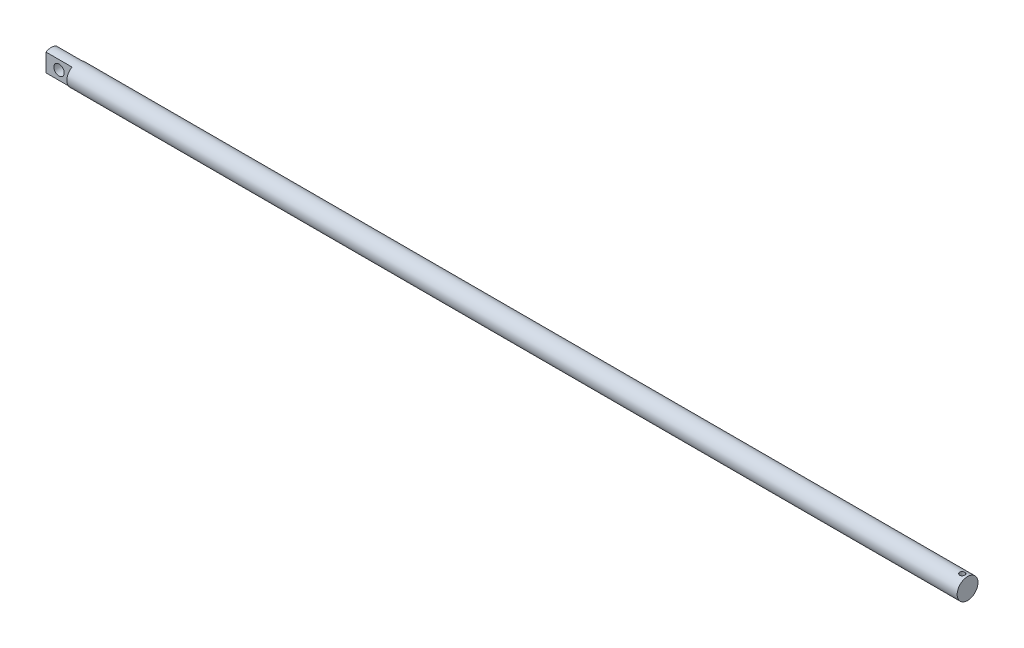
SolidWorks part; units mm, degrees
material "1060 合金"
ref_plane "前视基准面" through (0, 0, 0) normal (0, 0, 1) x (1, 0, 0)
ref_plane "上视基准面" through (0, 0, 0) normal (0, 1, 0) x (1, 0, 0)
ref_plane "右视基准面" through (0, 0, 0) normal (1, 0, 0) x (0, 0, -1)
sketch "草图1" plane through (0, 0, 0) normal (1, 0, 0) x (0, 0, -1)
  circle A0 centre (0, 0) radius 8
  dimension "D1" = 16
extrude "凸台-拉伸1" add sketch "草图1" along normal blind 703.5 contours A0
sketch "草图2" plane through (0, 0, 0) normal (0, 0, 1) x (1, 0, 0)
  line L0 (0, 8) -> (0, -8) construction
  line L2 (0, 0) -> (22.073, 0) construction
  circle A0 centre (10, 0) radius 4
  dimension "D1" = 8
  dimension "D3" = 10
extrude "切除-拉伸1" cut sketch "草图2" against normal through all and the other way through all
sketch "草图3" plane through (0, 0, 0) normal (-1, 0, 0) x (0, 0, 1)
  line L0 (-4, 10) -> (-4, -10)
  line L1 (-4, 10) -> (4, 10)
  line L2 (4, 10) -> (4, -10)
  line L3 (-4, -10) -> (4, -10)
  dimension "D1" = 4
  dimension "D2" = 4
  dimension "D3" = 20
  dimension "D4" = 10
extrude "切除-拉伸2" cut sketch "草图3" against normal blind 20 flip side to cut
sketch "草图4" plane through (0, 0, 0) normal (0, 1, 0) x (1, 0, 0)
  line L0 (703.5, -8) -> (703.5, 8) construction
  circle A0 centre (699.5, 0) radius 2
  dimension "D1" = 4
  dimension "D2" = 4
extrude "切除-拉伸3" cut sketch "草图4" against normal mid plane 50
equation "\"703。5\"=180"
